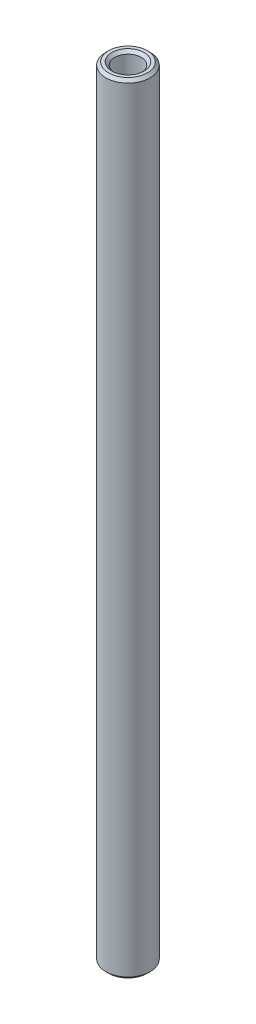
SolidWorks part; units mm, degrees
ref_plane "Front Plane" through (0, 0, 0) normal (0, 0, 1) x (1, 0, 0)
ref_plane "Top Plane" through (0, 0, 0) normal (0, 1, 0) x (1, 0, 0)
ref_plane "Right Plane" through (0, 0, 0) normal (1, 0, 0) x (0, 0, -1)
sketch "Sketch1" plane through (0, 0, 0) normal (0, 1, 0) x (1, 0, 0)
  circle A0 centre (0, 0) radius 1.9844
  circle A1 centre (0, 0) radius 1.1906
  dimension "D1" = 3.9688
  dimension "D2" = 0.7937
extrude "Boss-Extrude1" add sketch "Sketch1" along normal mid plane 69.85
chamfer "Chamfer1" distance 0.254 angle 45 4 edges at (0, -34.925, 1.1906) (0, -34.925, 1.9844) (0, 34.925, 1.1906) (0, 34.925, 1.9844)
